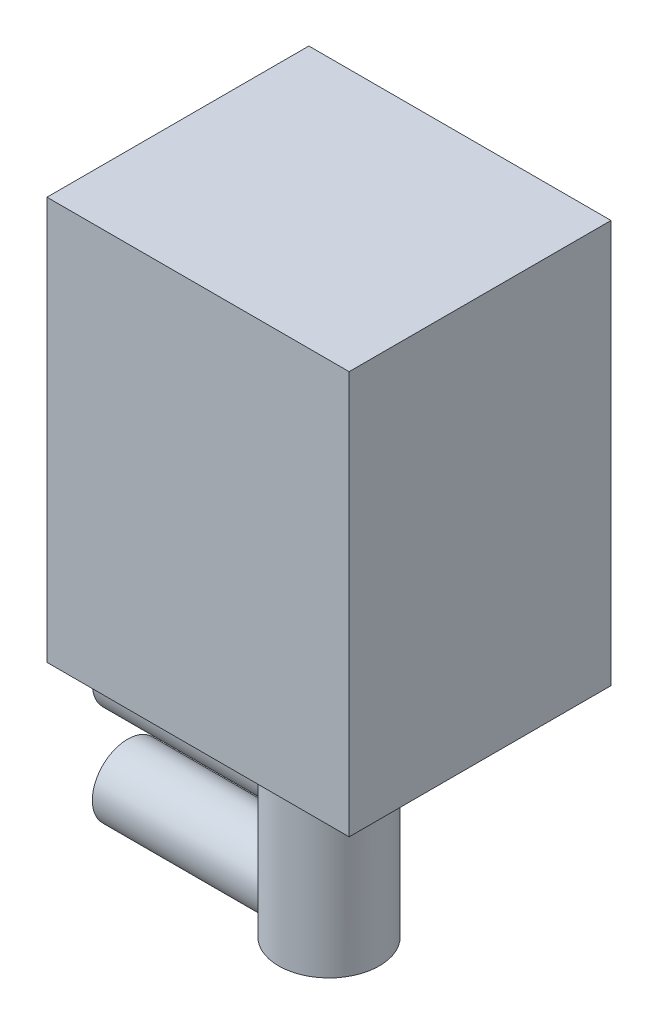
SolidWorks part; units mm, degrees
ref_plane "Front Plane" through (0, 0, 0) normal (1, 0, 0) x (0, 1, 0)
ref_plane "Top Plane" through (0, 0, 0) normal (0, 0, 1) x (0, 1, 0)
ref_plane "Right Plane" through (0, 0, 0) normal (0, 1, 0) x (-1, 0, 0)
sketch "Sketch1" plane through (0, 0, 0) normal (0, 0, 1) x (0, 1, 0)
  line L1 (0, 0) -> (-20, 0)
  line L2 (0, 0) -> (0, 15)
  line L3 (0, 15) -> (-20, 15)
  line L4 (-20, 0) -> (-20, 15)
  dimension "D1" = 20
  dimension "D2" = 15
extrude "Boss-Extrude1" add sketch "Sketch1" along normal blind 13
sketch "Sketch2" plane through (0, -20, 0) normal (0, -1, 0) x (1, 0, 0)
  line L1 (-15, 13) -> (-15, 0) construction
  line L2 (-15, 0) -> (0, 0) construction
  circle A0 centre (-7.5, 6.5) radius 2.5
  dimension "D1" = 5
  dimension "D2" = 7.5
  dimension "D3" = 6.5
extrude "Boss-Extrude2" add sketch "Sketch2" along normal blind 11.3
sketch "Sketch3" plane through (0, 0, 0) normal (1, 0, 0) x (0, 1, 0)
  line L0 (-31.3, 9) -> (-31.3, 4) construction
  line L1 (-31.3, 4) -> (-20, 4) construction
  circle A0 centre (-29.55, 6.5) radius 1.75
  circle A1 centre (-24.55, 6.5) radius 1.75
  point P8 (-24.55, 6.5)
  point P9 (0, 0)
  dimension "D1" = 3.5
  dimension "D2" = 5
  dimension "D3" = 2.5
extrude "Boss-Extrude3" add sketch "Sketch3" against normal blind 10 from offset 7.5
